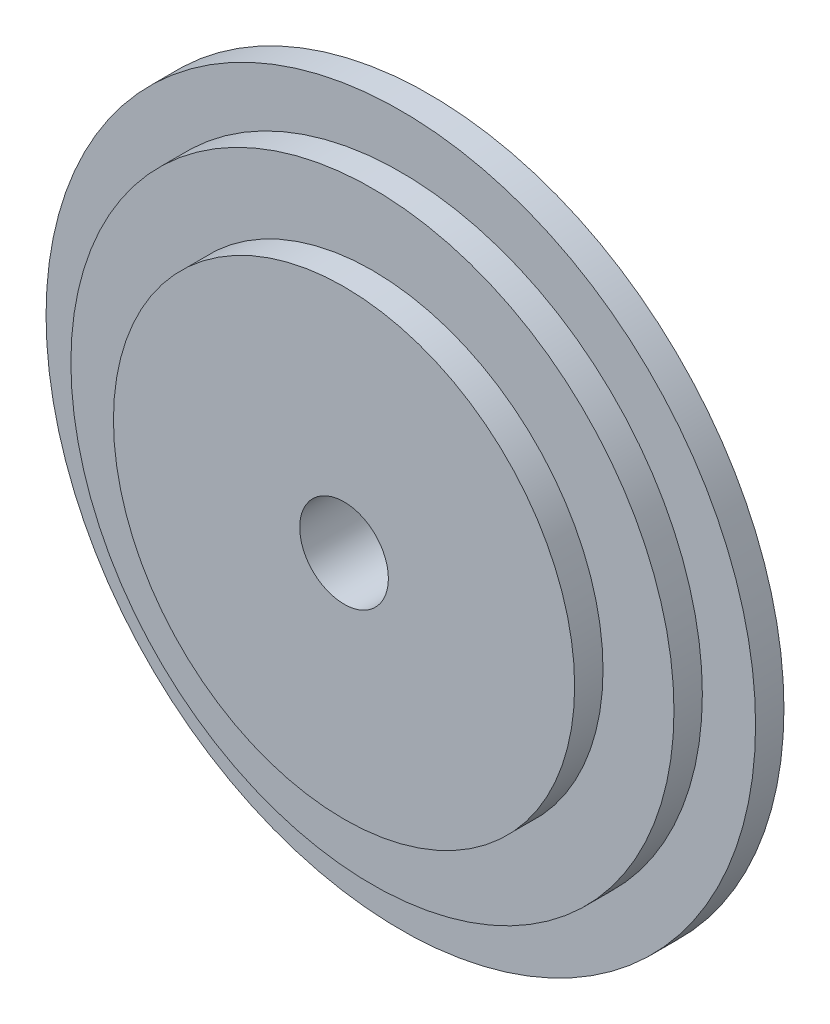
SolidWorks part; units mm, degrees
ref_plane "Frontal" through (0, 0, 0) normal (0, 0, 1) x (1, 0, 0)
ref_plane "Superior" through (0, 0, 0) normal (0, 1, 0) x (1, 0, 0)
ref_plane "Direito" through (0, 0, 0) normal (1, 0, 0) x (0, 0, -1)
sketch "Esboço1" plane through (0, 0, 0) normal (0, 0, 1) x (1, 0, 0)
  circle A0 centre (0, 0) radius 100
  point P62 (0, 0)
  dimension "D1" = 200
extrude "Ressalto-extrusão1" add sketch "Esboço1" along normal blind 8 contours A0
sketch "Esboço4" plane through (0, 0, 8) normal (0, 0, 1) x (1, 0, 0)
  circle A0 centre (0, 0) radius 85
  dimension "D1" = 170
extrude "Ressalto-extrusão2" add sketch "Esboço4" along normal blind 8
sketch "Esboço5" plane through (0, 0, 16) normal (0, 0, 1) x (1, 0, 0)
  circle A0 centre (0, 0) radius 65
  dimension "D1" = 130
extrude "Ressalto-extrusão4" add sketch "Esboço5" along normal blind 8 contours A0
sketch "Esboço6" plane through (0, 0, 24) normal (0, 0, 1) x (1, 0, 0)
  circle A0 centre (0, 0) radius 12.5
  dimension "D1" = 25
extrude "Corte-extrusão1" cut sketch "Esboço6" against normal through all
